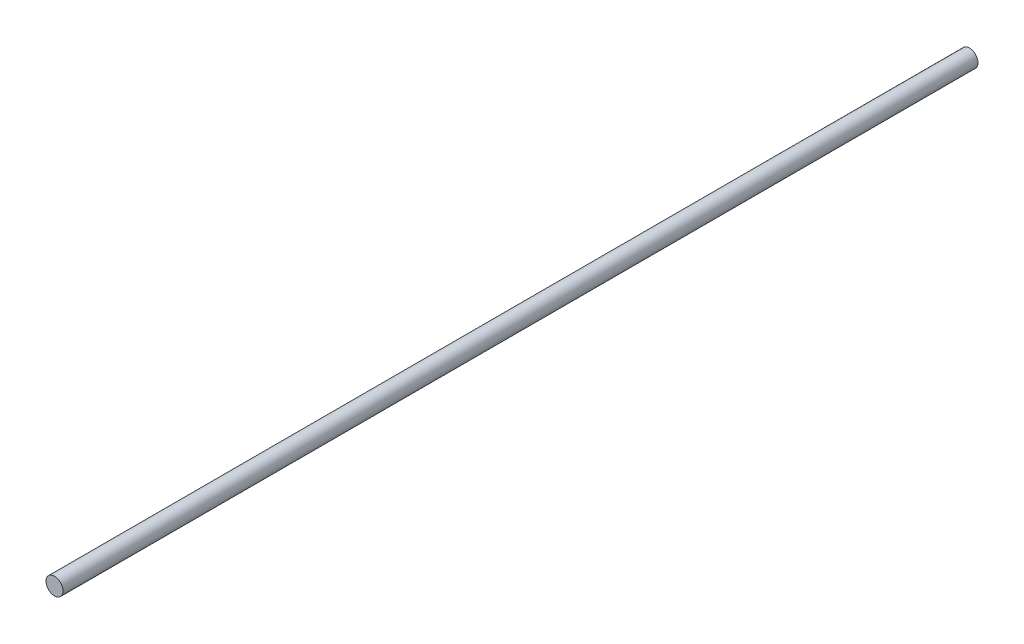
SolidWorks part; units mm, degrees
ref_plane "Plan de face" through (0, 0, 0) normal (0, 0, 1) x (1, 0, 0)
ref_plane "Plan de dessus" through (0, 0, 0) normal (0, 1, 0) x (1, 0, 0)
ref_plane "Plan de droite" through (0, 0, 0) normal (1, 0, 0) x (0, 0, -1)
sketch "Esquisse1" plane through (0, 0, 0) normal (0, 0, 1) x (1, 0, 0)
  circle A0 centre (0, 0) radius 4
  dimension "D1" = 8
extrude "Boss.-Extru.1" add sketch "Esquisse1" along normal blind 428
